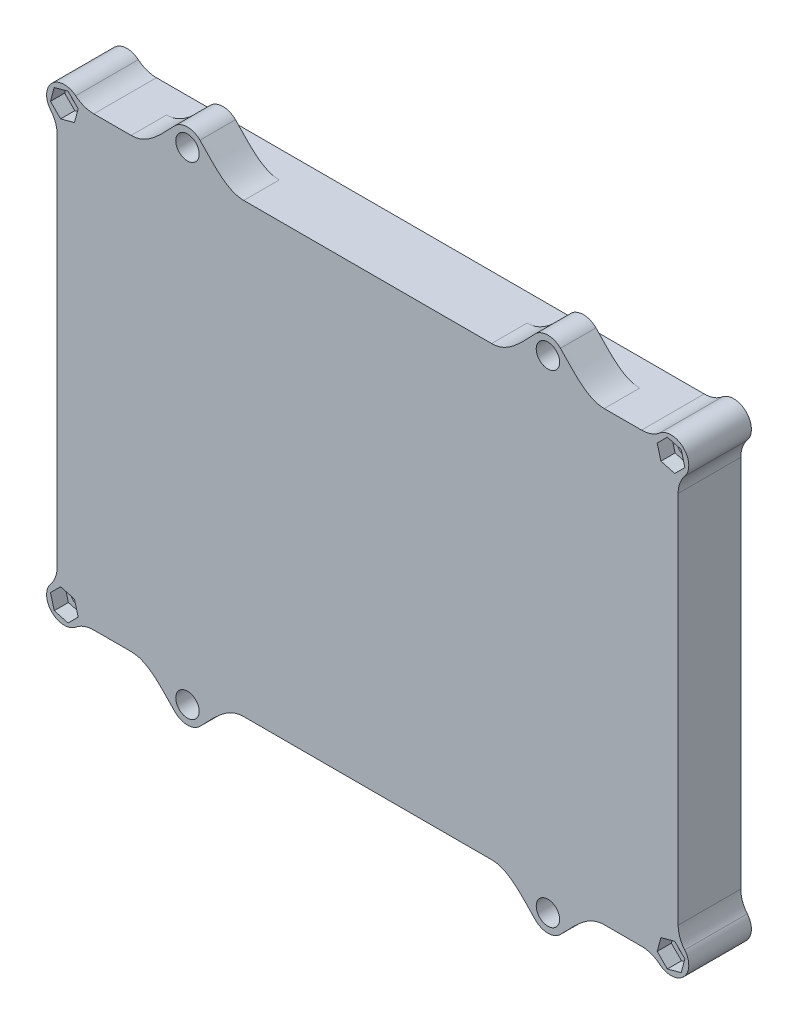
SolidWorks part; units mm, degrees
ref_plane "Front Plane" through (0, 0, 0) normal (0, 0, 1) x (1, 0, 0)
ref_plane "Top Plane" through (0, 0, 0) normal (0, 1, 0) x (1, 0, 0)
ref_plane "Right Plane" through (0, 0, 0) normal (1, 0, 0) x (0, 0, -1)
sketch "Sketch1" plane through (0, 0, 0) normal (0, 0, 1) x (1, 0, 0)
  line L1 (-148, -7) -> (7, -7) construction
  line L2 (7, -7) -> (7, 99) construction
  line L3 (7, 99) -> (-148, 99) construction
  line L4 (-148, 99) -> (-148, -7) construction
  line L5 (-148, -7) -> (7, -7) construction
  line L6 (7, -7) -> (7, 99) construction
  line L7 (7, 99) -> (-148, 99) construction
  line L8 (-148, 99) -> (-148, -7) construction
  line L9 (-158, -17) -> (17, -17)
  line L10 (17, -17) -> (17, 109)
  line L11 (17, 109) -> (-158, 109)
  line L12 (-158, 109) -> (-158, -17)
  dimension "D1" = 10
extrude "Boss-Extrude1" add sketch "Sketch1" along normal blind 2 from offset 2
sketch "Sketch2" plane through (0, 0, 2) normal (0, 0, -1) x (-1, 0, 0)
  circle A0 centre (0, 0) radius 5
  circle A1 centre (69.5, 63.5) radius 5
  circle A2 centre (0, 92) radius 5
  circle A3 centre (141, 92) radius 5
  circle A4 centre (141, 0) radius 5
  dimension "D1" = 10
extrude "Boss-Extrude2" add sketch "Sketch2" along normal up to surface (2 mm away)
fillet "Fillet1" radius 2 4 edges at (-158, -17, 3) (-158, 109, 3) (17, 109, 3) (17, -17, 3)
sketch "Sketch3" plane through (0, 0, 2) normal (0, 0, -1) x (-1, 0, 0)
  line L0 (-15, 109) -> (156, 109)
  line L1 (-15, 109) -> (156, 109)
  line L2 (-17, -15) -> (-17, 107)
  line L3 (-17, -15) -> (-17, 107)
  line L4 (156, -17) -> (-15, -17)
  line L5 (156, -17) -> (-15, -17)
  line L6 (158, 107) -> (158, -15)
  line L7 (158, 107) -> (158, -15)
  line L8 (-3, 102) -> (144, 102)
  line L9 (151, 95) -> (151, -3)
  line L10 (144, -10) -> (-3, -10)
  line L11 (-10, -3) -> (-10, 95)
  line L12 (151, 102) -> (151, -10) construction
  line L13 (-10, 102) -> (151, 102) construction
  line L14 (151, -10) -> (-10, -10) construction
  line L15 (-10, -10) -> (-10, 102) construction
  arc A0 (-15, 109) -> (-17, 107) centre (-15, 107) ccw
  arc A1 (-15, 109) -> (-17, 107) centre (-15, 107) ccw
  arc A2 (-17, -15) -> (-15, -17) centre (-15, -15) ccw
  arc A3 (-17, -15) -> (-15, -17) centre (-15, -15) ccw
  arc A4 (156, -17) -> (158, -15) centre (156, -15) ccw
  arc A5 (156, -17) -> (158, -15) centre (156, -15) ccw
  arc A6 (158, 107) -> (156, 109) centre (156, 107) ccw
  arc A7 (158, 107) -> (156, 109) centre (156, 107) ccw
  arc A8 (151, -3) -> (144, -10) centre (144, -3) cw
  arc A9 (-3, -10) -> (-10, -3) centre (-3, -3) cw
  arc A10 (-10, 95) -> (-3, 102) centre (-3, 95) cw
  arc A12 (151, 95) -> (144, 102) centre (144, 95) ccw
  arc A13 (151, 102) -> (151, 102) centre (151, 102) ccw construction
  arc A14 (151, -10) -> (151, -10) centre (151, -10) ccw construction
  arc A15 (-10, -10) -> (-10, -10) centre (-10, -10) ccw construction
  arc A16 (-10, 102) -> (-10, 102) centre (-10, 102) ccw construction
  dimension "D2" = 7
  dimension "D1" = 7
extrude "Boss-Extrude3" add sketch "Sketch3" along normal offset from surface (15.65 mm away) 2
sketch "Sketch5" plane through (0, 0, -13.65) normal (0, 0, -1) x (-1, 0, 0)
  line L0 (-10, -3) -> (-10, 95) construction
  line L1 (144, -10) -> (-3, -10) construction
  line L2 (-3, 102) -> (144, 102) construction
  line L3 (151, 95) -> (151, -3) construction
  line L4 (-10, -3) -> (-10, 95) construction
  line L5 (144, -10) -> (-3, -10) construction
  line L6 (-3, 102) -> (144, 102) construction
  line L7 (151, 95) -> (151, -3) construction
  line L8 (-3, 104) -> (144, 104)
  line L9 (153, 95) -> (153, -3)
  line L10 (144, -12) -> (-3, -12)
  line L11 (-12, -3) -> (-12, 95)
  arc A0 (-10, -3) -> (-3, -10) centre (-3, -3) ccw construction
  arc A1 (-3, 102) -> (-10, 95) centre (-3, 95) ccw construction
  arc A2 (144, -10) -> (151, -3) centre (144, -3) ccw construction
  arc A3 (151, 95) -> (144, 102) centre (144, 95) ccw construction
  arc A4 (-10, -3) -> (-3, -10) centre (-3, -3) ccw construction
  arc A5 (-3, 102) -> (-10, 95) centre (-3, 95) ccw construction
  arc A6 (144, -10) -> (151, -3) centre (144, -3) ccw construction
  arc A7 (151, 95) -> (144, 102) centre (144, 95) ccw construction
  arc A8 (153, 95) -> (144, 104) centre (144, 95) ccw
  arc A9 (144, -12) -> (153, -3) centre (144, -3) ccw
  arc A10 (-12, -3) -> (-3, -12) centre (-3, -3) ccw
  arc A11 (-3, 104) -> (-12, 95) centre (-3, 95) ccw
  dimension "D1" = 2
extrude "Cut-Extrude-Thin1" cut sketch "Sketch5" against normal blind 2.25 thin thin type one direction wall 3
sketch "Sketch8" plane through (0, 0, -13.65) normal (0, 0, -1) x (-1, 0, 0)
  circle A0 centre (156, 107) radius 5
  circle A2 centre (156, -15) radius 5
  circle A4 centre (-15, -15) radius 5
  circle A6 centre (-15, 107) radius 5
  dimension "D1" = 10
extrude "Boss-Extrude4" add sketch "Sketch8" against normal up to surface (17.65 mm away) up to face at (-70.5, 46, 4)
fillet "Fillet2" radius 8 8 edges at (-151.4174, -17, -4.825) (-158, -10.4174, -4.825) (-158, 102.4174, -4.825) (-151.4174, 109, -4.825) (10.4174, 109, -4.825) (17, 102.4174, -4.825) (17, -10.4174, -4.825) (10.4174, -17, -4.825)
sketch "Sketch9" plane through (0, 0, 0) normal (0, 0, -1) x (-1, 0, 0)
  circle A0 centre (0, 92) radius 1.5
  circle A1 centre (0, 0) radius 1.5
  circle A2 centre (69.5, 63.5) radius 1.5
  circle A3 centre (141, 92) radius 1.5
  circle A4 centre (141, 0) radius 1.5
  dimension "D1" = 3
extrude "Boss-Extrude5" add sketch "Sketch9" along normal blind 2
hole_wizard "M4 Clearance Hole1" positions "Sketch11" profile "Sketch10" hole size "M4" standard "ANSI Metric"
sketch "Sketch11" plane through (0, 0, -13.65) normal (0, 0, -1) x (-1, 0, 0)
  point P0 (-15, 107)
  point P3 (-15, -15)
  point P6 (156, -15)
  point P9 (156, 107)
sketch "Sketch10" plane through (15, 107, -13.65) normal (1, 0, 0) x (0, 1, 0)
  line L0 (0, 0) -> (0, 20.4019)
  line L1 (0, 20.4019) -> (2.25, 19.05)
  line L2 (2.25, 19.05) -> (2.25, 0)
  line L5 (2.25, 0) -> (0, 0)
  line L10 (0, 20.4019) -> (-2.25, 19.05) construction
  line L11 (0, -6.35) -> (0, 107.95) construction
  dimension "Hole Dia." = 4.5
  dimension "Hole Depth" = 19.05
  dimension "Drill Angle" = 118
sketch "Sketch12" plane through (0, 0, 4) normal (0, 0, 1) x (1, 0, 0)
  line L1 (17.8577, -17.8577) -> (18.9037, -13.954)
  line L2 (18.9037, -13.954) -> (16.046, -11.0963)
  line L3 (16.046, -11.0963) -> (12.1423, -12.1423)
  line L4 (12.1423, -12.1423) -> (11.0963, -16.046)
  line L5 (11.0963, -16.046) -> (13.954, -18.9037)
  line L6 (13.954, -18.9037) -> (17.8577, -17.8577)
  line L7 (17.8577, 109.8577) -> (13.954, 110.9037)
  line L8 (13.954, 110.9037) -> (11.0963, 108.046)
  line L9 (11.0963, 108.046) -> (12.1423, 104.1423)
  line L10 (12.1423, 104.1423) -> (16.046, 103.0963)
  line L11 (16.046, 103.0963) -> (18.9037, 105.954)
  line L12 (18.9037, 105.954) -> (17.8577, 109.8577)
  line L13 (-158.8577, 109.8577) -> (-159.9037, 105.954)
  line L14 (-159.9037, 105.954) -> (-157.046, 103.0963)
  line L15 (-157.046, 103.0963) -> (-153.1423, 104.1423)
  line L16 (-153.1423, 104.1423) -> (-152.0963, 108.046)
  line L17 (-152.0963, 108.046) -> (-154.954, 110.9037)
  line L18 (-154.954, 110.9037) -> (-158.8577, 109.8577)
  line L19 (-153.1423, -12.1423) -> (-157.046, -11.0963)
  line L20 (-157.046, -11.0963) -> (-159.9037, -13.954)
  line L21 (-159.9037, -13.954) -> (-158.8577, -17.8577)
  line L22 (-158.8577, -17.8577) -> (-154.954, -18.9037)
  line L23 (-154.954, -18.9037) -> (-152.0963, -16.046)
  line L24 (-152.0963, -16.046) -> (-153.1423, -12.1423)
  line L25 (-147.6934, -17) -> (6.6934, -17) construction
  line L26 (6.6934, 109) -> (-147.6934, 109) construction
  circle A0 centre (15, -15) radius 3.5 construction
  circle A1 centre (15, 107) radius 3.5 construction
  circle A2 centre (-156, 107) radius 3.5 construction
  circle A3 centre (-156, -15) radius 3.5 construction
  dimension "D1" = 7
  dimension "D2" = 135
  dimension "D3" = 135
  dimension "D4" = 135
  dimension "D5" = 135
  dimension "D6" = 7
  dimension "D7" = 7
  dimension "D8" = 7
extrude "Cut-Extrude1" cut sketch "Sketch12" against normal blind 4
fillet "Fillet3" radius 1 13 edges at (-136, 0, 2) (5, 92, 2) (5, 0, 2) (-64.5, 63.5, 2) (-136, 92, 2) (-148.9497, -7.9497, 2) (-70.5, -10, 2) (7.9497, -7.9497, 2) (10, 46, 2) (7.9497, 99.9497, 2) (-70.5, 102, 2) (-148.9497, 99.9497, 2) (-151, 46, 2)
sketch "Sketch13" plane through (0, 0, 4) normal (0, 0, 1) x (1, 0, 0)
  line L1 (-70.5, 46) -> (-70.5, 0) construction
  line L2 (-121.3, -22) -> (-117.7645, -25.5355) construction
  line L3 (-121.3, -22) -> (-124.8355, -25.5355) construction
  line L4 (-105.425, -17) -> (-137.175, -17)
  line L5 (17, 46) -> (-158, 46) construction
  line L6 (17, -6.6934) -> (17, 98.6934) construction
  line L7 (-158, 98.6934) -> (-158, -6.6934) construction
  line L8 (-45.1, 46) -> (-45.1, -5.9466) construction
  line L9 (-95.9, 46) -> (-95.9, 1.3063) construction
  line L10 (-19.7, -22) -> (-16.1645, -25.5355) construction
  line L11 (-19.7, -22) -> (-23.2355, -25.5355) construction
  line L12 (-35.575, -17) -> (-3.825, -17)
  line L13 (-19.7, 114) -> (-23.2355, 117.5355) construction
  line L14 (-19.7, 114) -> (-16.1645, 117.5355) construction
  line L15 (-121.3, 114) -> (-124.8355, 117.5355) construction
  line L16 (-121.3, 114) -> (-117.7645, 117.5355) construction
  line L17 (-35.575, 109) -> (-3.825, 109)
  line L18 (-105.425, 109) -> (-137.175, 109)
  arc A0 (-124.8355, -25.5355) -> (-117.7645, -25.5355) centre (-121.3, -22) ccw
  arc A1 (-16.1645, -25.5355) -> (-23.2355, -25.5355) centre (-19.7, -22) cw
  arc A2 (-16.1645, 117.5355) -> (-23.2355, 117.5355) centre (-19.7, 114) ccw
  arc A3 (-124.8355, 117.5355) -> (-117.7645, 117.5355) centre (-121.3, 114) cw
  spline S0 degree 3 poles (-105.425, -17) (-110.4263, -17) (-114.228, -21.9991) (-117.7645, -25.5355) knots 0 0 0 0 1 1 1 1
  spline S1 degree 3 poles (-137.175, -17) (-132.1737, -17) (-128.372, -21.9991) (-124.8355, -25.5355) knots 0 0 0 0 1 1 1 1
  spline S2 degree 3 poles (-3.825, -17) (-8.8263, -17) (-12.628, -21.9991) (-16.1645, -25.5355) knots 0 0 0 0 1 1 1 1
  spline S3 degree 3 poles (-35.575, -17) (-30.5737, -17) (-26.772, -21.9991) (-23.2355, -25.5355) knots 0 0 0 0 1 1 1 1
  spline S4 degree 3 poles (-35.575, 109) (-30.5737, 109) (-26.772, 113.9991) (-23.2355, 117.5355) knots 0 0 0 0 1 1 1 1
  spline S5 degree 3 poles (-3.825, 109) (-8.8263, 109) (-12.628, 113.9991) (-16.1645, 117.5355) knots 0 0 0 0 1 1 1 1
  spline S6 degree 3 poles (-137.175, 109) (-132.1737, 109) (-128.372, 113.9991) (-124.8355, 117.5355) knots 0 0 0 0 1 1 1 1
  spline S7 degree 3 poles (-105.425, 109) (-110.4263, 109) (-114.228, 113.9991) (-117.7645, 117.5355) knots 0 0 0 0 1 1 1 1
  dimension "D5" = 25.4
  dimension "D6" = 25.4
extrude "Boss-Extrude6" add sketch "Sketch13" against normal blind 10
hole_wizard "M6 Clearance Hole2" positions "Sketch17" profile "Sketch16" hole size "M6" standard "ANSI Metric"
sketch "Sketch17" plane through (0, 0, -6) normal (0, 0, -1) x (-1, 0, 0)
  point P0 (19.7, 114)
  point P3 (121.3, 114)
  point P6 (121.3, -22)
  point P9 (19.7, -22)
sketch "Sketch16" plane through (-19.7, 114, -6) normal (1, 0, 0) x (0, 1, 0)
  line L0 (0, 0) -> (0, 21.0328)
  line L1 (0, 21.0328) -> (3.3, 19.05)
  line L2 (3.3, 19.05) -> (3.3, 0)
  line L5 (3.3, 0) -> (0, 0)
  line L10 (0, 21.0328) -> (-3.3, 19.05) construction
  line L11 (0, -6.35) -> (0, 107.95) construction
  dimension "Hole Dia." = 6.6
  dimension "Hole Depth" = 19.05
  dimension "Drill Angle" = 118
